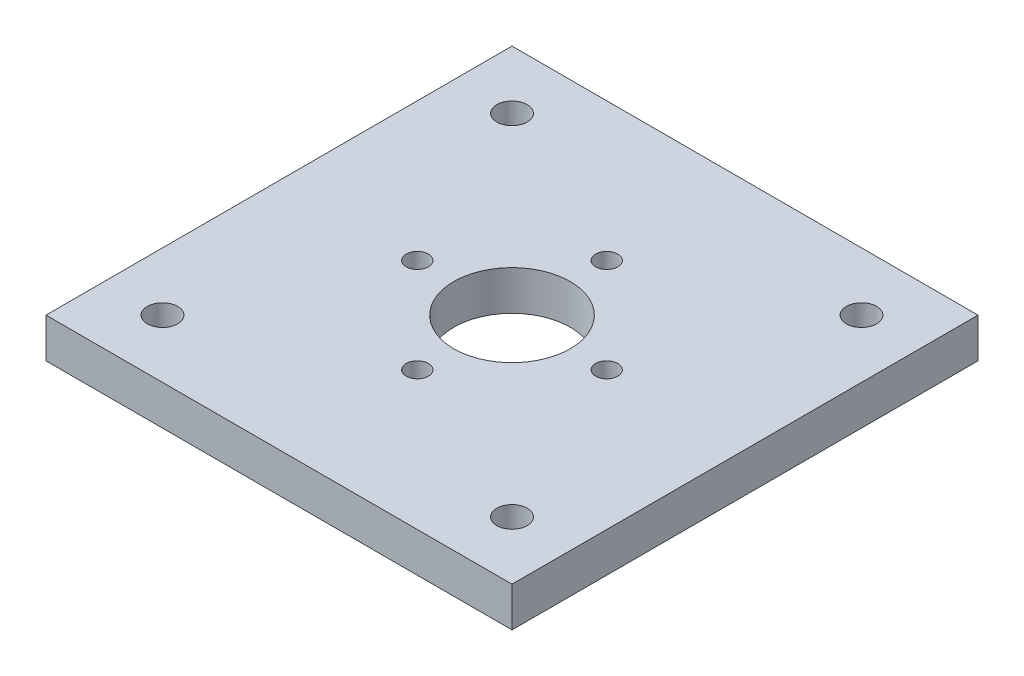
SolidWorks part; units mm, degrees
material "AISI 1020"
ref_plane "Front Plane" through (0, 0, 0) normal (0, 0, 1) x (1, 0, 0)
ref_plane "Top Plane" through (0, 0, 0) normal (0, 1, 0) x (1, 0, 0)
ref_plane "Right Plane" through (0, 0, 0) normal (1, 0, 0) x (0, 0, -1)
sketch "Sketch1" plane through (0, 0, 0) normal (0, 1, 0) x (1, 0, 0)
  line L0 (0, 200) -> (0, -200) construction
  line L1 (-200, 200) -> (200, 200)
  line L2 (-200, 200) -> (-200, -200)
  line L3 (-200, -200) -> (200, -200)
  line L4 (200, 200) -> (200, -200)
  line L5 (-200, 200) -> (200, -200) construction
  line L6 (-200, -200) -> (200, 200) construction
  line L7 (-200, 0) -> (200, 0) construction
  circle A0 centre (-150, 150) radius 13
  circle A1 centre (-150, -150) radius 13
  circle A2 centre (150, -150) radius 13
  circle A3 centre (150, 150) radius 13
  circle A4 centre (0, 0) radius 50
  circle A5 centre (0, 81.3) radius 9.5
  circle A6 centre (-81.3, 0) radius 9.5
  circle A8 centre (0, -81.3) radius 9.5
  circle A9 centre (81.3, 0) radius 9.5
  point P0 (0, 0)
  dimension "D3" = 26
  dimension "D5" = 100
  dimension "D6" = 19
  dimension "D1" = 400
  dimension "D2" = 400
  dimension "D4" = 300
extrude "Boss-Extrude1" add sketch "Sketch1" along normal blind 34
